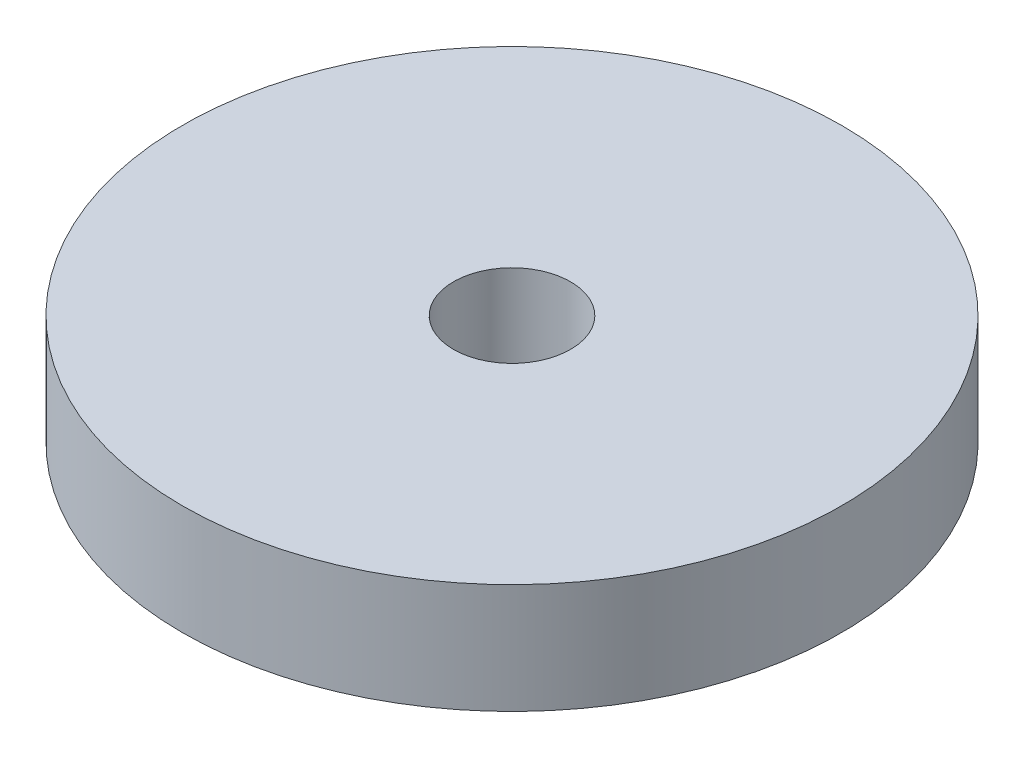
SolidWorks part; units mm, degrees
ref_plane "Front Plane" through (0, 0, 0) normal (0, 0, 1) x (1, 0, 0)
ref_plane "Top Plane" through (0, 0, 0) normal (0, 1, 0) x (1, 0, 0)
ref_plane "Right Plane" through (0, 0, 0) normal (1, 0, 0) x (0, 0, -1)
sketch "Sketch1" plane through (0, 0, 0) normal (0, 1, 0) x (1, 0, 0)
  circle A0 centre (0, 0) radius 9
  circle A1 centre (0, 0) radius 1.6
  dimension "D1" = 3.2
  dimension "D2" = 18
extrude "Boss-Extrude1" add sketch "Sketch1" along normal blind 3
